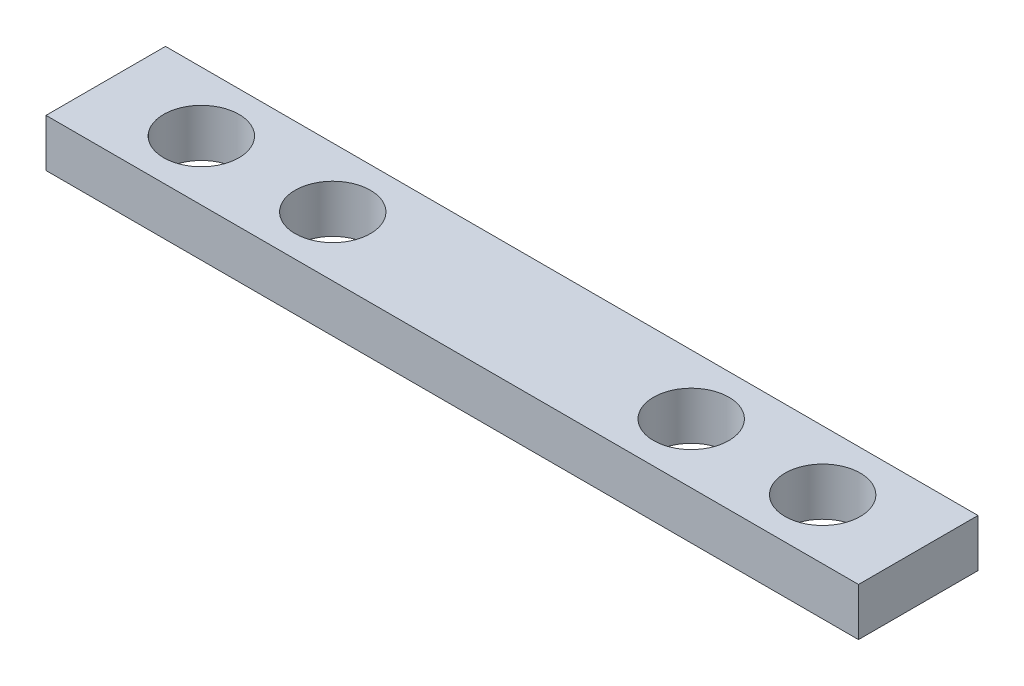
SolidWorks part; units mm, degrees
ref_plane "Front Plane" through (0, 0, 0) normal (0, 0, 1) x (1, 0, 0)
ref_plane "Top Plane" through (0, 0, 0) normal (0, 1, 0) x (1, 0, 0)
ref_plane "Right Plane" through (0, 0, 0) normal (1, 0, 0) x (0, 0, -1)
sketch "Sketch1" plane through (0, 0, 0) normal (0, 1, 0) x (1, 0, 0)
  line L1 (-17, -2.5) -> (17, -2.5)
  line L2 (-17, -2.5) -> (-17, 2.5)
  line L3 (-17, 2.5) -> (17, 2.5)
  line L4 (17, -2.5) -> (17, 2.5)
  line L5 (-17, -2.5) -> (17, 2.5) construction
  line L6 (-17, 2.5) -> (17, -2.5) construction
  point P0 (0, 0)
  dimension "D1" = 5
  dimension "D2" = 34
extrude "Boss-Extrude2" add sketch "Sketch1" along normal blind 2
sketch "Sketch4" plane through (0, 2, 0) normal (0, 1, 0) x (1, 0, 0)
  line L0 (-17, 2.5) -> (-17, -2.5) construction
  line L1 (17, -2.5) -> (17, 2.5) construction
  circle A0 centre (-13, 0) radius 1.575
  circle A1 centre (13, 0) radius 1.575
  dimension "D1" = 3.15
  dimension "D2" = 3.15
  dimension "D3" = 4
  dimension "D4" = 4
extrude "Cut-Extrude3" cut sketch "Sketch4" against normal blind 2
sketch "Sketch5" plane through (0, 2, 0) normal (0, 1, 0) x (1, 0, 0)
  circle A0 centre (-7.5, 0) radius 1.575
  circle A1 centre (7.5, 0) radius 1.575
  dimension "D1" = 3.15
  dimension "D2" = 3.15
  dimension "D3" = 15
  dimension "D4" = 7.5
extrude "Cut-Extrude4" cut sketch "Sketch5" against normal blind 2
equation "\"D4@Sketch5\"=\"D3@Sketch5\"/2"
